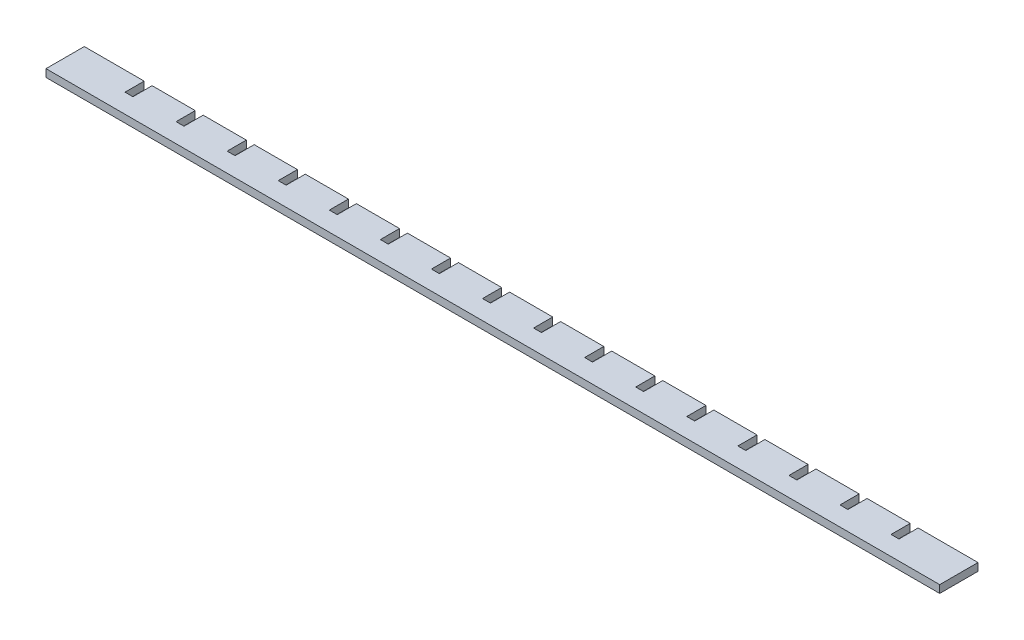
SolidWorks part; units mm, degrees
ref_plane "Ebene vorne" through (0, 0, 0) normal (0, 0, 1) x (1, 0, 0)
ref_plane "Ebene oben" through (0, 0, 0) normal (0, 1, 0) x (1, 0, 0)
ref_plane "Ebene rechts" through (0, 0, 0) normal (1, 0, 0) x (0, 0, -1)
sketch "Skizze1" plane through (0, 0, 0) normal (0, 1, 0) x (1, 0, 0)
  line L0 (-109.3802, 10.5189) -> (-109.3802, 3.0189)
  line L1 (-152.8302, 10.5189) -> (-129.3802, 10.5189)
  line L2 (-152.8302, 10.5189) -> (-152.8302, -4.4811)
  line L3 (-152.8302, -4.4811) -> (197.1698, -4.4811)
  line L4 (197.1698, 10.5189) -> (197.1698, -4.4811)
  line L6 (-129.3802, 10.5189) -> (-129.3802, 3.0189)
  line L7 (-129.3802, 3.0189) -> (-126.2802, 3.0189)
  line L8 (-126.2802, 10.5189) -> (-126.2802, 3.0189)
  line L9 (-109.3802, 3.0189) -> (-106.2802, 3.0189)
  line L10 (-106.2802, 10.5189) -> (-106.2802, 3.0189)
  line L11 (-89.3802, 10.5189) -> (-89.3802, 3.0189)
  line L12 (-89.3802, 3.0189) -> (-86.2802, 3.0189)
  line L13 (-86.2802, 10.5189) -> (-86.2802, 3.0189)
  line L14 (-69.3802, 10.5189) -> (-69.3802, 3.0189)
  line L15 (-69.3802, 3.0189) -> (-66.2802, 3.0189)
  line L16 (-66.2802, 10.5189) -> (-66.2802, 3.0189)
  line L17 (-49.3802, 10.5189) -> (-49.3802, 3.0189)
  line L18 (-49.3802, 3.0189) -> (-46.2802, 3.0189)
  line L19 (-46.2802, 10.5189) -> (-46.2802, 3.0189)
  line L20 (-29.3802, 10.5189) -> (-29.3802, 3.0189)
  line L21 (-29.3802, 3.0189) -> (-26.2802, 3.0189)
  line L22 (-26.2802, 10.5189) -> (-26.2802, 3.0189)
  line L23 (-9.3802, 10.5189) -> (-9.3802, 3.0189)
  line L24 (-9.3802, 3.0189) -> (-6.2802, 3.0189)
  line L25 (-6.2802, 10.5189) -> (-6.2802, 3.0189)
  line L26 (10.6198, 10.5189) -> (10.6198, 3.0189)
  line L27 (10.6198, 3.0189) -> (13.7198, 3.0189)
  line L28 (13.7198, 10.5189) -> (13.7198, 3.0189)
  line L29 (30.6198, 10.5189) -> (30.6198, 3.0189)
  line L30 (30.6198, 3.0189) -> (33.7198, 3.0189)
  line L31 (33.7198, 10.5189) -> (33.7198, 3.0189)
  line L32 (50.6198, 10.5189) -> (50.6198, 3.0189)
  line L33 (50.6198, 3.0189) -> (53.7198, 3.0189)
  line L34 (53.7198, 10.5189) -> (53.7198, 3.0189)
  line L35 (70.6198, 10.5189) -> (70.6198, 3.0189)
  line L36 (70.6198, 3.0189) -> (73.7198, 3.0189)
  line L37 (73.7198, 10.5189) -> (73.7198, 3.0189)
  line L38 (90.6198, 10.5189) -> (90.6198, 3.0189)
  line L39 (90.6198, 3.0189) -> (93.7198, 3.0189)
  line L40 (93.7198, 10.5189) -> (93.7198, 3.0189)
  line L41 (110.6198, 10.5189) -> (110.6198, 3.0189)
  line L42 (110.6198, 3.0189) -> (113.7198, 3.0189)
  line L43 (113.7198, 10.5189) -> (113.7198, 3.0189)
  line L44 (130.6198, 10.5189) -> (130.6198, 3.0189)
  line L45 (130.6198, 3.0189) -> (133.7198, 3.0189)
  line L46 (133.7198, 10.5189) -> (133.7198, 3.0189)
  line L47 (150.6198, 10.5189) -> (150.6198, 3.0189)
  line L48 (150.6198, 3.0189) -> (153.7198, 3.0189)
  line L49 (153.7198, 10.5189) -> (153.7198, 3.0189)
  line L50 (170.6198, 10.5189) -> (170.6198, 3.0189)
  line L51 (170.6198, 3.0189) -> (173.7198, 3.0189)
  line L52 (173.7198, 10.5189) -> (173.7198, 3.0189)
  line L53 (-126.2802, 10.5189) -> (-89.3802, 10.5189)
  line L54 (-86.2802, 10.5189) -> (-69.3802, 10.5189)
  line L55 (-66.2802, 10.5189) -> (-49.3802, 10.5189)
  line L56 (-46.2802, 10.5189) -> (-29.3802, 10.5189)
  line L57 (-26.2802, 10.5189) -> (-9.3802, 10.5189)
  line L58 (-6.2802, 10.5189) -> (10.6198, 10.5189)
  line L59 (33.7198, 10.5189) -> (50.6198, 10.5189)
  line L60 (13.7198, 10.5189) -> (30.6198, 10.5189)
  line L61 (53.7198, 10.5189) -> (70.6198, 10.5189)
  line L62 (73.7198, 10.5189) -> (90.6198, 10.5189)
  line L63 (93.7198, 10.5189) -> (110.6198, 10.5189)
  line L64 (113.7198, 10.5189) -> (130.6198, 10.5189)
  line L65 (133.7198, 10.5189) -> (150.6198, 10.5189)
  line L66 (173.7198, 10.5189) -> (197.1698, 10.5189)
  line L67 (153.7198, 10.5189) -> (170.6198, 10.5189)
  dimension "D1" = 350
  dimension "D2" = 15
  dimension "D3" = 3.1
  dimension "D4" = 23.45
  dimension "D6" = 7.5
  dimension "D5" = 16
extrude "Aufsatz-Linear austragen1" add sketch "Skizze1" along normal blind 3 contours L67 L49 L48 L47 L65 L46 L45 L44 L64 L43 L42 L41 L63 L40 L39 L38 L62 L37 L36 L35 L61 L34 L33 L32 L59 L31 L30 L29 L60 L28 L27 L26 L58 L25 L24 L23 L57 L22 L21 L20 L56 L19 L18 L17 L55 L16 L15 L14 L54 L13 L12
